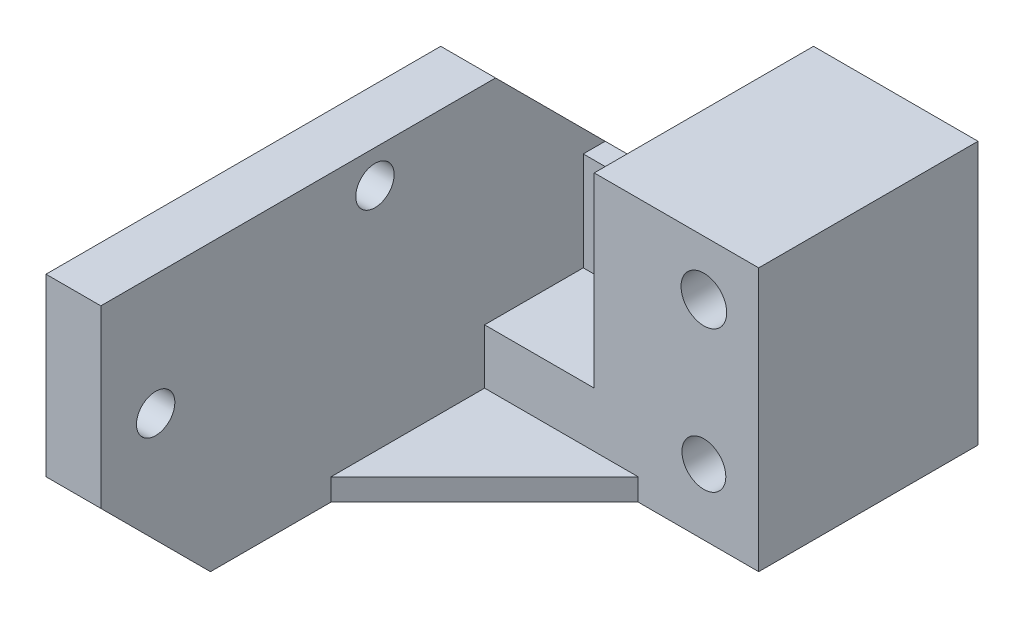
SolidWorks part; units mm, degrees
ref_plane "Спереди" through (0, 0, 0) normal (0, 0, 1) x (1, 0, 0)
ref_plane "Сверху" through (0, 0, 0) normal (0, 1, 0) x (1, 0, 0)
ref_plane "Справа" through (0, 0, 0) normal (1, 0, 0) x (0, 0, -1)
sketch "Эскиз1" plane through (0, 0, 0) normal (0, 1, 0) x (1, 0, 0)
  line L0 (0, 0) -> (0, 11)
  line L1 (0, 11) -> (15, 11)
  line L2 (15, 11) -> (15, 20)
  line L3 (15, 20) -> (30, 20)
  line L4 (30, 20) -> (30, 0)
  line L5 (30, 0) -> (0, 0)
  dimension "D1" = 20
  dimension "D2" = 9
  dimension "D3" = 15
  dimension "D4" = 15
extrude "Бобышка-Вытянуть1" add sketch "Эскиз1" along normal blind 12
sketch "Эскиз2" plane through (0, 0, 0) normal (0, 0, 1) x (1, 0, 0)
  line L0 (30, 6) -> (0, 6) construction
  line L1 (30, 12) -> (30, 0) construction
  line L2 (0, 12) -> (0, 0) construction
  circle A0 centre (25, 6) radius 2
  dimension "D1" = 5
  dimension "D2" = 4
extrude "Вырез-Вытянуть1" cut sketch "Эскиз2" against normal up to next
sketch "Эскиз3" plane through (0, 0, 0) normal (-1, 0, 0) x (0, 0, 1)
  line L0 (0, 12) -> (0, 0) construction
  line L1 (-11, 0) -> (35, 0)
  line L2 (-11, 0) -> (-11, 26)
  line L3 (-11, 26) -> (35, 26)
  line L4 (35, 0) -> (35, 26)
  line L5 (-11, 12) -> (0, 12) construction
  circle A0 centre (30, 15) radius 1.75
  circle A1 centre (10, 23) radius 1.75
  dimension "D3" = 11
  dimension "D6" = 5
  dimension "D7" = 3.5
  dimension "D1" = 35
  dimension "D2" = 14
  dimension "D4" = 11
  dimension "D5" = 10
extrude "Бобышка-Вытянуть2" add sketch "Эскиз3" against normal blind 5
chamfer "Фаска1" distance 10 angle 45 1 edges at (2.5, 26, -11)
sketch "Эскиз4" plane through (0, 0, 0) normal (0, -1, 0) x (1, 0, 0)
  line L0 (5, 14) -> (19, 0)
  line L1 (5, 0) -> (5, 35) construction
  line L2 (5, 0) -> (30, 0) construction
  line L3 (19, 0) -> (5, 0)
  line L4 (5, 0) -> (5, 14)
  dimension "D1" = 14
extrude "Бобышка-Вытянуть3" add sketch "Эскиз4" against normal blind 2
chamfer "Фаска2" distance 10 angle 45 1 edges at (2.5, 0, 35)
sketch "Эскиз5" plane through (0, 12, 0) normal (0, 1, 0) x (1, 0, 0)
  line L1 (15, 20) -> (30, 20)
  line L2 (15, 20) -> (15, 0)
  line L3 (15, 0) -> (30, 0)
  line L4 (30, 20) -> (30, 0)
extrude "Бобышка-Вытянуть4" add sketch "Эскиз5" along normal blind 12
sketch "Эскиз6" plane through (0, 0, 0) normal (0, 0, 1) x (1, 0, 0)
  line L0 (25, 19) -> (25, 6) construction
  line L3 (15, 24) -> (30, 24) construction
  circle A0 centre (25, 19) radius 2.0841
  dimension "D1" = 5
extrude "Вырез-Вытянуть2" cut sketch "Эскиз6" against normal through all
sketch "Эскиз7" plane through (0, 0, -11) normal (0, 0, -1) x (-1, 0, 0)
  line L0 (-15, 24) -> (-15, 0) construction
  line L1 (-15, 12) -> (-5, 12)
  line L2 (-15, 12) -> (-15, 7)
  line L3 (-15, 7) -> (-5, 7)
  line L4 (-5, 12) -> (-5, 7)
  dimension "D1" = 5
extrude "Вырез-Вытянуть3" cut sketch "Эскиз7" against normal through all
sketch "Эскиз8" plane through (0, 0, -11) normal (0, 0, -1) x (-1, 0, 0)
  line L1 (-5, 16) -> (-15, 16)
  line L2 (-5, 16) -> (-5, 7)
  line L3 (-5, 7) -> (-15, 7)
  line L4 (-15, 16) -> (-15, 7)
extrude "Бобышка-Вытянуть5" add sketch "Эскиз8" against normal blind 2
chamfer "Фаска3" distance 4 angle 45 2 edges at (0, 8, -11) (7.5, 0, -11)
